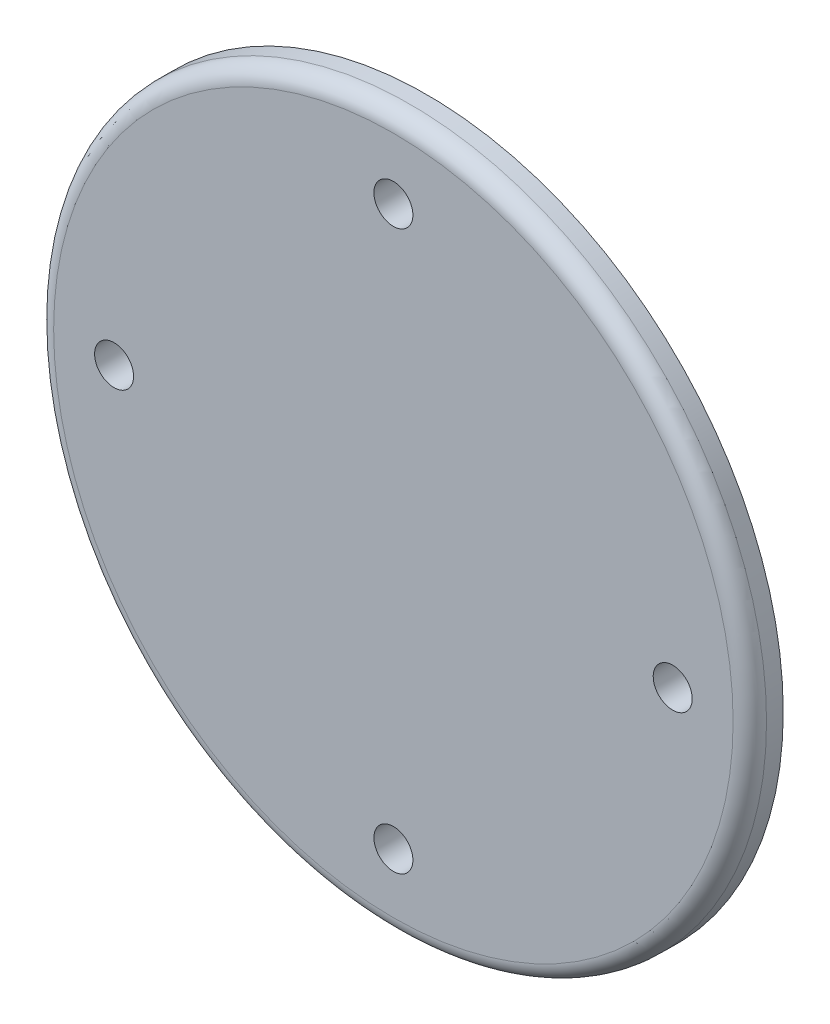
SolidWorks part; units mm, degrees
ref_plane "Přední rovina" through (0, 0, 0) normal (0, 0, 1) x (1, 0, 0)
ref_plane "Vrchní rovina" through (0, 0, 0) normal (0, 1, 0) x (1, 0, 0)
ref_plane "Pravá rovina" through (0, 0, 0) normal (1, 0, 0) x (0, 0, -1)
sketch "Skica1" plane through (0, 0, 0) normal (1, 0, 0) x (0, 0, -1)
  line L0 (0, 64) -> (0, 0)
  line L1 (0, 64) -> (6, 64)
  line L2 (6, 64) -> (6, 34)
  line L3 (6, 34) -> (16, 34)
  line L4 (16, 34) -> (16, 29)
  line L5 (16, 29) -> (6, 29)
  line L6 (6, 29) -> (6, 0)
  line L7 (-30.7823, 0) -> (56.3044, 0) construction
  line L8 (0, 0) -> (6, 0)
  dimension "D1" = 128
  dimension "D2" = 68
  dimension "D3" = 58
  dimension "D4" = 10
  dimension "D5" = 6
revolve "Rotovat1" add sketch "Skica1" angle 360 about L7
sketch "Skica2" plane through (0, 0, 0) normal (0, 0, 1) x (1, 0, 0)
  circle A0 centre (0, 0) radius 50 construction
  circle A1 centre (0, 50) radius 3.5
  dimension "D1" = 7
  dimension "D2" = 100
extrude "Odebrat vysunutím1" cut sketch "Skica2" against normal up to next (6 mm away)
pattern_circular "Kruhové pole1" count 4 over 360 about axis through (0, -0.15, 0) along (0, 0, 1) of "Odebrat vysunutím1"
fillet "Zaoblit1" radius 3 1 edges at (64, 0, 0)
fillet "Zaoblit2" radius 1 1 edges at (34, 0, -6)
fillet "Zaoblit3" radius 5 1 edges at (29, 0, -6)
